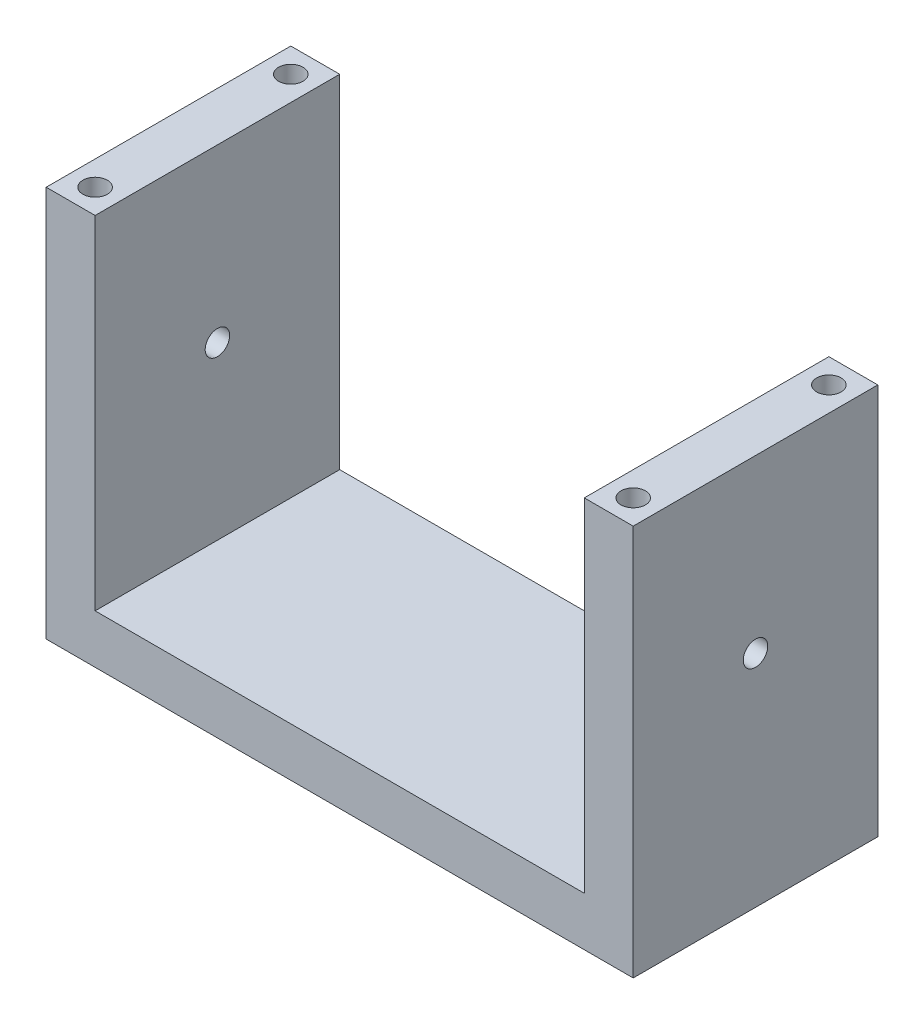
SolidWorks part; units mm, degrees
material "Acrylic (Medium-high impact)"
ref_plane "Front Plane" through (0, 0, 0) normal (0, 0, 1) x (1, 0, 0)
ref_plane "Top Plane" through (0, 0, 0) normal (0, 1, 0) x (1, 0, 0)
ref_plane "Right Plane" through (0, 0, 0) normal (1, 0, 0) x (0, 0, -1)
sketch "Sketch1" plane through (0, 0, 0) normal (0, 0, 1) x (1, 0, 0)
  line L0 (-6, 8) -> (-5, 8)
  line L1 (-5, 8) -> (-5, 1)
  line L2 (-5, 1) -> (5, 1)
  line L3 (5, 1) -> (5, 8)
  line L4 (5, 8) -> (6, 8)
  line L5 (6, 8) -> (6, 0)
  line L6 (6, 0) -> (-6, 0)
  line L7 (-6, 0) -> (-6, 8)
  dimension "D1" = 10
  dimension "D2" = 12
  dimension "D3" = 1
  dimension "D4" = 0
  dimension "D5" = 6
  dimension "D6" = 8
  dimension "D7" = 8
  dimension "D8" = 7
extrude "Boss-Extrude1" add sketch "Sketch1" along normal blind 5
sketch "Sketch2" plane through (0, 0, 0) normal (0, -1, 0) x (1, 0, 0)
  line L0 (6, 5) -> (6, 0) construction
  line L1 (-6, 5) -> (6, 5) construction
  line L2 (-6, 0) -> (6, 0) construction
  line L3 (-6, 5) -> (-6, 0) construction
  circle A0 centre (-5.5, 4.5) radius 0.25
  circle A1 centre (-5.5, 0.5) radius 0.25
  circle A2 centre (5.5, 4.5) radius 0.25
  circle A3 centre (5.5, 0.5) radius 0.25
  point P0 (-5.5, 4.5)
  point P1 (-5.5, 0.5)
  point P2 (5.5, 0.5)
  point P3 (5.5, 4.5)
  dimension "D9" = 0.5
  dimension "D1" = 0.5
  dimension "D2" = 0.5
  dimension "D3" = 0.5
  dimension "D4" = 0.5
  dimension "D5" = 0.5
  dimension "D6" = 0.5
  dimension "D7" = 0.5
  dimension "D8" = 0.5
extrude "Cut-Extrude1" cut sketch "Sketch2" against normal through all
sketch "Sketch4" plane through (0, 0, 0) normal (1, 0, 0) x (0, 0, -1)
  line L0 (-5, 0) -> (-5, 8) construction
  line L3 (-5, 8) -> (0, 8) construction
  circle A0 centre (-2.5, 4.5) radius 0.25
  dimension "D1" = 2.5
  dimension "D3" = 0.5
  dimension "D2" = 3.5
extrude "Cut-Extrude2" cut sketch "Sketch4" against normal blind 10 and the other way blind 10
